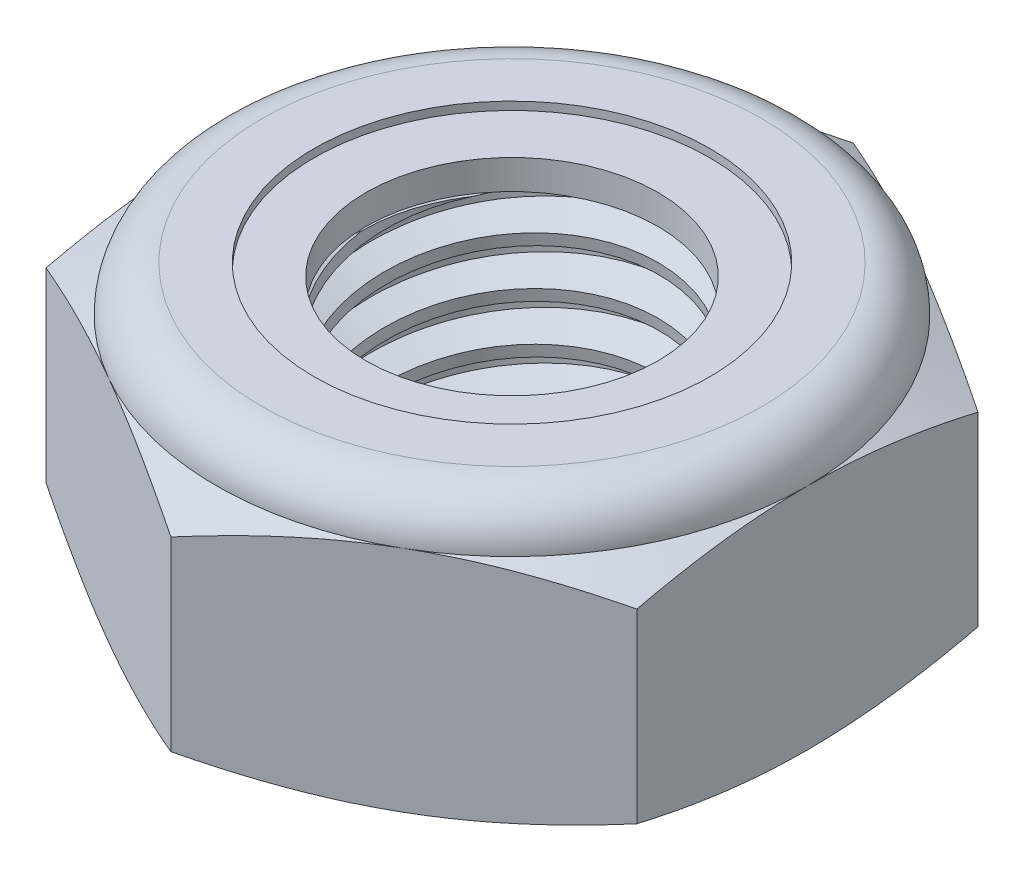
SolidWorks part; units mm, degrees
ref_plane "Front" through (0, 0, 0) normal (0, 0, 1) x (1, 0, 0)
ref_plane "Top" through (0, 0, 0) normal (0, 1, 0) x (1, 0, 0)
ref_plane "Right" through (0, 0, 0) normal (1, 0, 0) x (0, 0, -1)
sketch "Sketch1" plane through (0, 0, 0) normal (0, 1, 0) x (1, 0, 0)
  line L1 (0, 6.4158) -> (-5.5563, 3.2079)
  line L2 (-5.5563, 3.2079) -> (-5.5563, -3.2079)
  line L3 (-5.5563, -3.2079) -> (0, -6.4158)
  line L4 (0, -6.4158) -> (5.5562, -3.2079)
  line L5 (5.5562, -3.2079) -> (5.5562, 3.2079)
  line L6 (5.5562, 3.2079) -> (0, 6.4158)
  circle A0 centre (0, 0) radius 5.5563 construction
  dimension "Hex Flats" = 11.1125
extrude "Extrude1" add sketch "Sketch1" along normal blind 5.1594
sketch "Sketch2" plane through (0, 0, 0) normal (1, 0, 0) x (0, 0, -1)
  line L0 (-3.175, 0) -> (-3.175, 5.1594) construction
  line L1 (0, 0) -> (3.175, 0)
  line L2 (0, 0) -> (0, 5.1594)
  line L3 (0, 5.1594) -> (3.175, 5.1594)
  line L4 (3.175, 0) -> (3.175, 5.1594)
  line L5 (-3.2079, 5.1594) -> (3.2079, 5.1594) construction
  line L7 (0, -3.175) -> (0, 0) construction
  dimension "Thread Dia" = 6.35
revolve "Revolve1" add sketch "Sketch2" angle 360 about L7
sketch "Sketch3" plane through (0, 0, 0) normal (1, 0, 0) x (0, 0, -1)
  line L0 (3.175, 5.1594) -> (-3.175, 5.1594) construction
  line L1 (-3.175, 5.1594) -> (-3.175, 4.2522) construction
  line L2 (-3.175, 4.2522) -> (3.175, 5.1594) construction
  line L3 (3.175, 5.1594) -> (3.191, 5.0471) construction
  line L4 (3.191, 5.0471) -> (3.3033, 4.2613)
  line L5 (3.3033, 4.2613) -> (2.7771, 4.4725)
  line L6 (2.7771, 4.4725) -> (2.7451, 4.6971)
  line L7 (2.7451, 4.6971) -> (3.191, 5.0471)
  line L8 (2.7611, 4.5848) -> (3.2472, 4.6542) construction
  line L9 (3.175, 5.1594) -> (3.175, 4.6439) construction
  line L10 (3.175, 4.6439) -> (-3.175, 3.7368) construction
  line L11 (-3.175, 3.7368) -> (-3.175, 4.2522) construction
  line L12 (-0.1384, 5.1594) -> (0.1384, 3.2213) construction
  line L13 (-3.175, 0) -> (-3.175, 5.1594) construction
  line L14 (0, 5.1594) -> (3.175, 5.1594) construction
  line L15 (3.175, 0) -> (3.175, 5.1594) construction
  point P13 (0, 4.1904)
  dimension "D1" = 0.1134
  dimension "D2" = 0.2268
  dimension "Thread Pitch" = 0.9071
  dimension "D4" = 60
  dimension "D5" = 0.9071
revolve "Cut-Revolve1" cut sketch "Sketch3" angle 360 about L12
pattern_linear "LPattern1" count 6 spacing 0.9071 along (0, -1, 0) count 2 spacing 0.9071 along (0, 1, 0) of "Cut-Revolve1"
sketch "Sketch4" plane through (0, 0, 0) normal (1, 0, 0) x (0, 0, -1)
  line L0 (0, 5.1594) -> (3.175, 5.1594)
  line L1 (3.175, 5.1594) -> (2.7451, 4.9589)
  line L2 (2.7451, 4.9589) -> (2.7451, 0.2005)
  line L3 (2.7451, 0.2005) -> (3.175, 0)
  line L4 (3.175, 0) -> (0, 0)
  line L5 (0, 0) -> (0, 5.1594)
  line L6 (3.175, 0) -> (3.175, 5.1594) construction
  line L7 (0, 5.1594) -> (3.175, 5.1594) construction
  line L8 (0, 0) -> (3.175, 0) construction
  line L9 (0, 0) -> (0, 5.1594) construction
  line L10 (0, 5.1594) -> (0, 5.6338) construction
  dimension "D1" = 25
revolve "Cut-Revolve2" cut sketch "Sketch4" angle 360 about L10
combine bodies "Combine1" operation type subtract main body 112 bodies to subtract 111
sketch "Sketch5" plane through (0, 0, 0) normal (1, 0, 0) x (0, 0, -1)
  line L0 (0, 0) -> (5.5563, 0)
  line L1 (5.5563, 0) -> (6.4158, 0.4008)
  line L2 (6.4158, 0.4008) -> (6.4158, 3.8987)
  line L3 (6.4158, 3.8987) -> (5.5562, 4.2995)
  line L4 (4.6964, 5.1594) -> (4.6964, 6.4294)
  line L5 (4.6964, 6.4294) -> (7.6858, 6.4294)
  line L6 (7.6858, 6.4294) -> (7.6858, -1.27)
  line L7 (7.6858, -1.27) -> (0, -1.27)
  line L8 (0, -1.27) -> (0, 0)
  line L9 (5.5562, 4.2995) -> (5.5563, 0) construction
  line L10 (0, 0) -> (3.175, 0) construction
  line L13 (6.4158, 2.1497) -> (7.6858, 2.1497) construction
  line L14 (6.4158, 5.1594) -> (6.4158, 0) construction
  line L15 (0, 0) -> (0, 6.4294) construction
  line L20 (0, 6.4294) -> (4.6964, 6.4294) construction
  line L22 (0, 5.1594) -> (3.175, 5.1594) construction
  arc A0 (5.5562, 4.2995) -> (4.6964, 5.1594) centre (4.6964, 4.2995) ccw
  dimension "D1" = 25
  dimension "D2" = 1.27
  dimension "D3" = 5.1594
  dimension "D4" = 0.8599
revolve "Cut-Revolve3" cut sketch "Sketch5" angle 360 about L15
sketch "Sketch6" plane through (0, 0, 0) normal (1, 0, 0) x (0, 0, -1)
  line L0 (0, 4.2995) -> (5.4039, 4.2995)
  line L1 (4.6964, 5.007) -> (3.7207, 5.007)
  line L2 (0, 6.4294) -> (0, 4.2995)
  line L3 (3.7207, 6.4294) -> (0, 6.4294)
  line L4 (0, 6.4294) -> (4.6964, 6.4294) construction
  line L5 (0, 0) -> (0, 6.4294) construction
  line L6 (0, 6.4294) -> (0, 44.323) construction
  line L7 (3.7207, 5.007) -> (3.7207, 6.4294)
  line L8 (4.6964, 5.1594) -> (4.6964, 5.007) construction
  line L9 (3.7207, 5.007) -> (2.7451, 5.007) construction
  line L10 (2.7451, 5.007) -> (2.7451, 4.9589) construction
  arc A0 (5.4039, 4.2995) -> (4.6964, 5.007) centre (4.6964, 4.2995) ccw
  arc A1 (5.5562, 4.2995) -> (4.6964, 5.1594) centre (4.6964, 4.2995) ccw construction
  dimension "D1" = 0.1524
revolve "Cut-Revolve4" cut sketch "Sketch6" angle 360 about L6
sketch "Sketch7" plane through (0, 0, 0) normal (1, 0, 0) x (0, 0, -1)
  line L0 (2.7451, 4.3757) -> (5.323, 4.3757)
  line L1 (4.6964, 4.9308) -> (2.7451, 4.9308)
  line L2 (2.7451, 4.9308) -> (2.7451, 4.3757)
  line L3 (2.7451, 4.3757) -> (0, 4.3757) construction
  line L4 (0, 4.3757) -> (0, 4.9308) construction
  line L5 (0, 4.9308) -> (2.7451, 4.9308) construction
  line L6 (2.7451, 4.3757) -> (2.7451, 4.2995) construction
  line L7 (0, 4.2995) -> (5.4039, 4.2995) construction
  line L8 (4.6964, 4.9308) -> (4.6964, 5.007) construction
  arc A0 (5.323, 4.3757) -> (4.6964, 4.9308) centre (4.6964, 4.2995) ccw
  arc A2 (5.4039, 4.2995) -> (4.6964, 5.007) centre (4.6964, 4.2995) ccw construction
  dimension "D1" = 0.0762
revolve "Revolve2" add sketch "Sketch7" angle 360 about L4
equation "\"D1@Sketch3\"=\"Thread Pitch@Sketch3\"/8"
equation "\"D2@Sketch3\"=\"Thread Pitch@Sketch3\"/4"
equation "\"D5@Sketch3\"=\"Thread Pitch@Sketch3\""
equation "\"D4@LPattern1\"=\"Thread Pitch@Sketch3\""
equation "\"D3@LPattern1\"=\"Thread Pitch@Sketch3\""
equation "\"D1@LPattern1\"=\"Height@Extrude1\"/\"Thread Pitch@Sketch3\""
equation "\"D4@Sketch5\"=\"Height@Extrude1\"/6"
